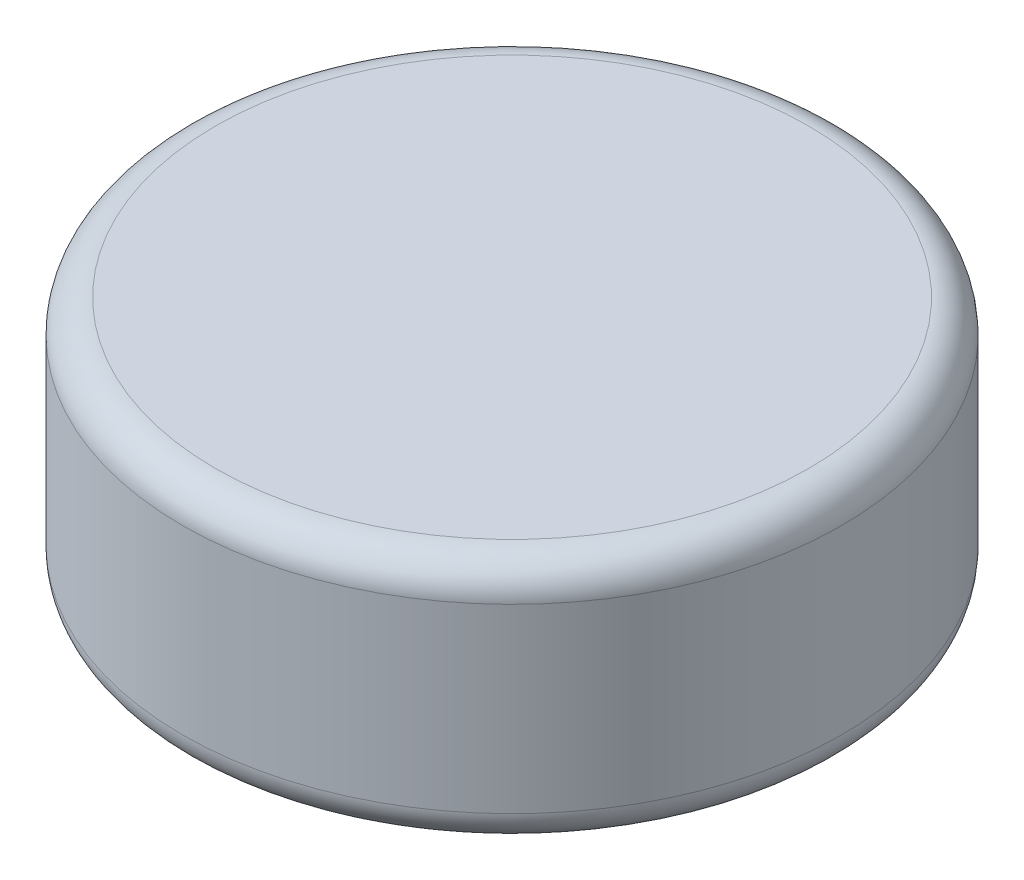
SolidWorks part; units mm, degrees
material "Alloy Steel (SS)"
ref_plane "Front Plane" through (0, 0, 0) normal (0, 0, 1) x (1, 0, 0)
ref_plane "Top Plane" through (0, 0, 0) normal (0, 1, 0) x (1, 0, 0)
ref_plane "Right Plane" through (0, 0, 0) normal (1, 0, 0) x (0, 0, -1)
sketch "Sketch1" plane through (0, 0, 0) normal (0, 1, 0) x (1, 0, 0)
  circle A0 centre (0, 0) radius 2
  dimension "D1" = 4
extrude "Boss-Extrude1" add sketch "Sketch1" along normal blind 1.5
fillet "Fillet1" radius 0.2 2 edges at (0, 0, 2) (0, 1.5, 2)
